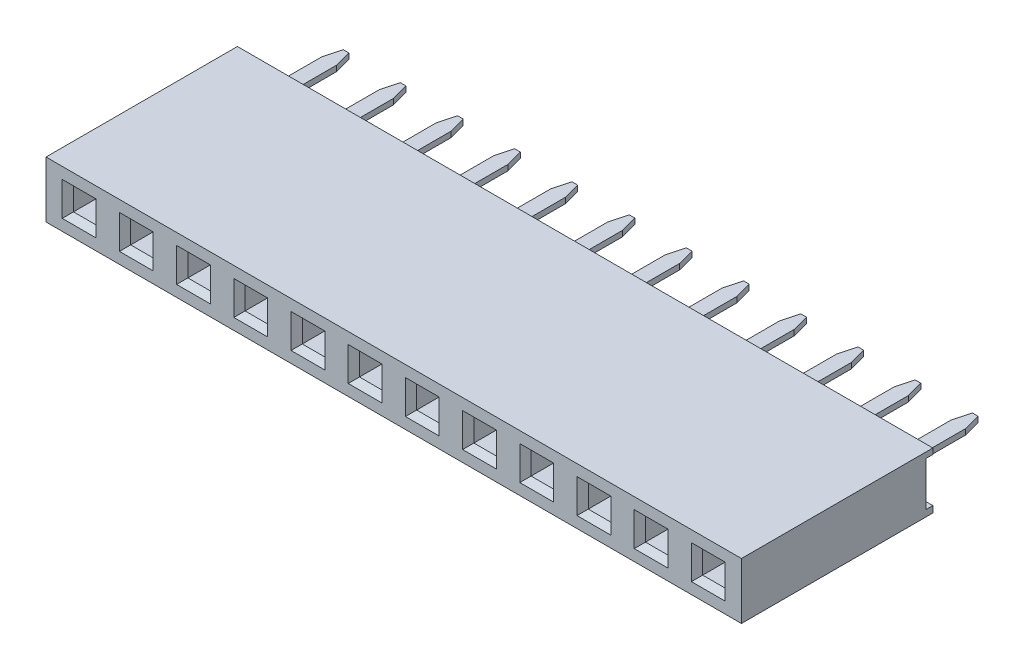
SolidWorks part; units mm, degrees
ref_plane "Front Plane" through (0, 0, 0) normal (0, 0, 1) x (1, 0, 0)
ref_plane "Top Plane" through (0, 0, 0) normal (0, 1, 0) x (1, 0, 0)
ref_plane "Right Plane" through (0, 0, 0) normal (1, 0, 0) x (0, 0, -1)
sketch "Sketch1" plane through (0, 0, 0) normal (0, 0, 1) x (1, 0, 0)
  line L1 (0, 0) -> (30.88, 0)
  line L2 (0, 0) -> (0, 2.5)
  line L3 (0, 2.5) -> (30.88, 2.5)
  line L4 (30.88, 0) -> (30.88, 2.5)
  dimension "width" = 2.5
  dimension "length" = 30.88
extrude "Boss-Extrude1" add sketch "Sketch1" along normal blind 8.5
sketch "Sketch2" plane through (0, 0, 8.5) normal (0, 0, 1) x (1, 0, 0)
  line L0 (0, 1.25) -> (30.88, 1.25) construction
  line L1 (0, 2.5) -> (0, 0) construction
  line L2 (30.88, 0) -> (30.88, 2.5) construction
  line L3 (0, 0) -> (30.88, 0) construction
  line L5 (30.88, 2.5) -> (0, 2.5) construction
  line L6 (1.47, 2.5) -> (1.47, 0) construction
  line L7 (0.97, 1.75) -> (1.97, 1.75)
  line L8 (0.97, 1.75) -> (0.97, 0.75)
  line L9 (0.97, 0.75) -> (1.97, 0.75)
  line L10 (1.97, 1.75) -> (1.97, 0.75)
  point P16 (1.47, 1.75)
  point P17 (1.97, 1.25)
  dimension "D1" = 1.25
  dimension "D2" = 1.47
  dimension "D3" = 1
  dimension "D4" = 1
extrude "Cut-Extrude1" cut sketch "Sketch2" against normal blind 2.25
chamfer "Chamfer1" distance 0.25 angle 45 4 edges at (0.97, 1.25, 8.5) (1.47, 0.75, 8.5) (1.97, 1.25, 8.5) (1.47, 1.75, 8.5)
sketch "Sketch3" plane through (0, 0, 0) normal (-1, 0, 0) x (0, 0, 1)
  line L0 (0, 2.5) -> (0, 0) construction
  line L1 (0, 2.25) -> (0.3, 2.25)
  line L2 (0, 2.25) -> (0, 0.2861)
  line L3 (0, 0.2861) -> (0.3, 0.2861)
  line L4 (0.3, 2.25) -> (0.3, 0.2861)
  line L5 (8.5, 1.25) -> (0, 1.2681) construction
  line L6 (8.5, 2.5) -> (0, 2.5) construction
  line L7 (8.5, 2.5) -> (8.5, 0) construction
  dimension "D1" = 0.25
  dimension "D2" = 0.3
extrude "Cut-Extrude2" cut sketch "Sketch3" against normal through all
ref_plane "Plane1" through (0, 1.25, 0) normal (0, -1, 0) x (-1, 0, 0)
sketch "Sketch4" plane through (0, 1.25, 0) normal (0, -1, 0) x (-1, 0, 0)
  line L0 (-1.47, -8.25) -> (-1.47, -0.3) construction
  line L1 (-0.97, -8.25) -> (-1.97, -8.25) construction
  line L2 (-30.88, -0.3) -> (0, -0.3) construction
  line L3 (0, 0) -> (-30.88, 0) construction
  line L4 (-1.795, -0.3) -> (-1.145, -0.3)
  line L5 (-1.795, -0.3) -> (-1.795, 3.35)
  line L6 (-1.795, 3.35) -> (-1.145, 3.35)
  line L7 (-1.145, -0.3) -> (-1.145, 3.35)
  point P10 (-1.47, -0.3)
  dimension "D1" = 0.65
  dimension "D2" = 3.35
extrude "Boss-Extrude2" add sketch "Sketch4" along normal mid plane 0.25 separate body
chamfer "Chamfer2" distance 0.2 angle 75 2 edges at (1.145, 1.25, -3.35) (1.795, 1.25, -3.35)
pattern_linear "LPattern4" count 12 spacing 2.54 along (1, 0, 0) of bodies 104
pattern_linear "LPattern5" count 12 spacing 2.54 along (1, 0, 0) of "Cut-Extrude1", "Chamfer1"
equation "\"pins\"= 12"
equation "\"rows\"= 1"
equation "\"length\"= 2.54 * \"pins\" + .4"
equation "\"width\"= 2.5 * \"rows\""
equation "\"width@Sketch1\"= 2.5 * \"rows\""
equation "\"length@Sketch1\"= 2.54 * \"pins\" + .4"
equation "\"D2@LPattern5\"= \"rows\""
equation "\"D2@LPattern4\"= \"rows\""
equation "\"D1@LPattern4\"= \"pins\""
equation "\"D1@LPattern5\"= \"pins\""
